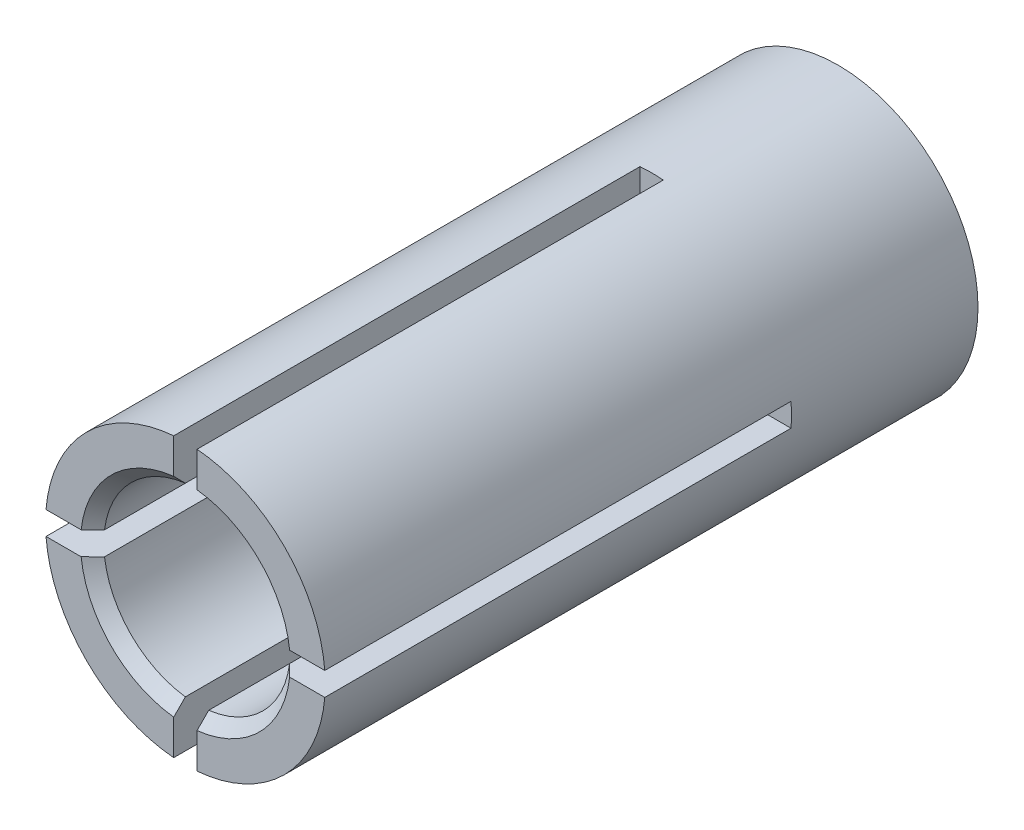
SolidWorks part; units mm, degrees
ref_plane "Face" through (0, 0, 0) normal (0, 0, 1) x (1, 0, 0)
ref_plane "Dessus" through (0, 0, 0) normal (0, 1, 0) x (1, 0, 0)
ref_plane "Droite" through (0, 0, 0) normal (1, 0, 0) x (0, 0, -1)
sketch "Esquisse1" plane through (0, 0, 0) normal (0, 0, 1) x (1, 0, 0)
  circle A0 centre (0, 0) radius 3
  circle A1 centre (0, 0) radius 2
  dimension "D1" = 6
  dimension "D2" = 4
extrude "Extrusion1" add sketch "Esquisse1" along normal blind 14
chamfer "Chanfrein1" distance 0.25 angle 45 1 edges at (2, 0, 14)
sketch "Esquisse4" plane through (0, 0, 14) normal (0, 0, 1) x (1, 0, 0)
  line L0 (3, 0) -> (-3, 0) construction
  line L1 (0, -3) -> (0, 3) construction
  line L2 (0.25, 2.9896) -> (0.25, 0.25)
  line L3 (0.25, 0.25) -> (2.9896, 0.25)
  line L4 (2.9896, -0.25) -> (0.25, -0.25)
  line L5 (0.25, -0.25) -> (0.25, -2.9896)
  line L6 (-2.9896, -0.25) -> (-0.25, -0.25)
  line L7 (-0.25, -0.25) -> (-0.25, -2.9896)
  line L8 (-2.9896, 0.25) -> (-0.25, 0.25)
  line L9 (-0.25, 0.25) -> (-0.25, 2.9896)
  circle A0 centre (0, 0) radius 3 construction
  arc A1 (2.9896, 0.25) -> (2.9896, -0.25) centre (0, 0) cw
  arc A2 (0.25, -2.9896) -> (-0.25, -2.9896) centre (0, 0) cw
  arc A3 (-2.9896, -0.25) -> (-2.9896, 0.25) centre (0, 0) cw
  arc A4 (-0.25, 2.9896) -> (0.25, 2.9896) centre (0, 0) cw
  dimension "D1" = 0.25
  dimension "D2" = 0.25
  dimension "D3" = 0.25
extrude "Enlèv. mat.-Extru.1" cut sketch "Esquisse4" against normal blind 10
